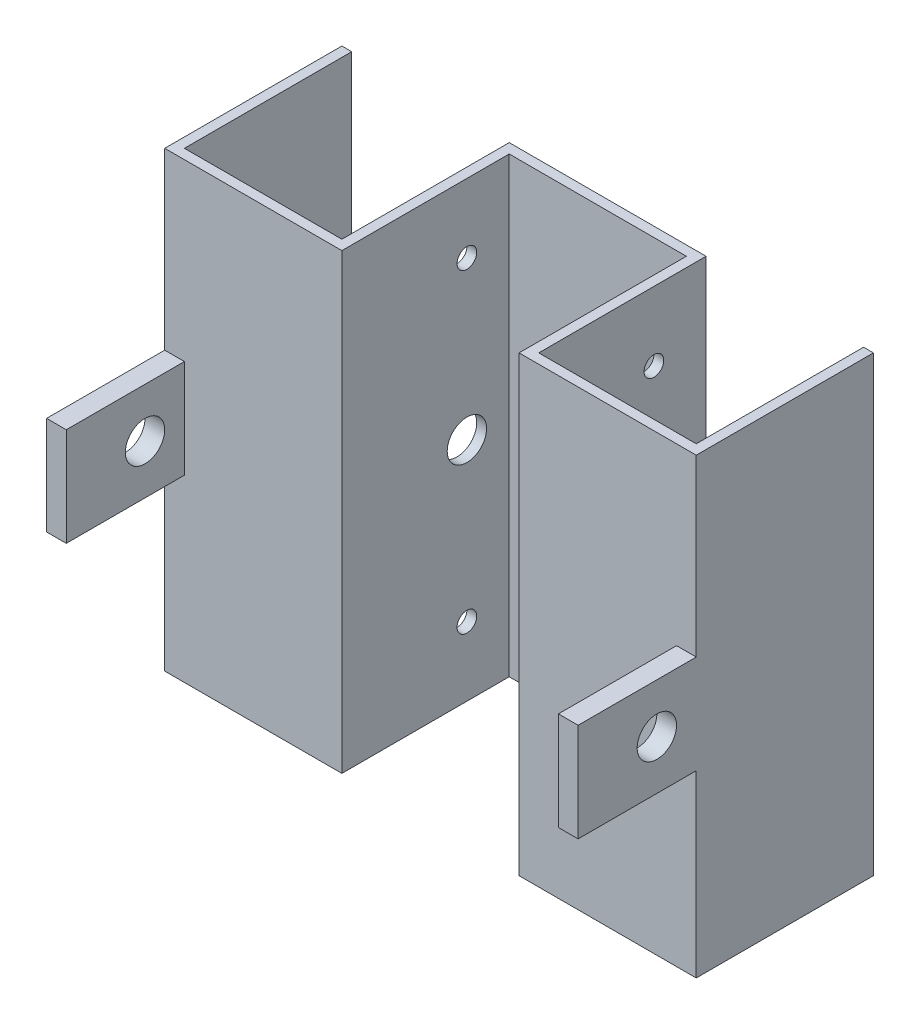
SolidWorks part; units mm, degrees
ref_plane "Plan de face" through (0, 0, 0) normal (0, 0, 1) x (1, 0, 0)
ref_plane "Plan de dessus" through (0, 0, 0) normal (0, 1, 0) x (1, 0, 0)
ref_plane "Plan de droite" through (0, 0, 0) normal (1, 0, 0) x (0, 0, -1)
sketch "Esquisse1" plane through (0, 0, 0) normal (0, 0, 1) x (1, 0, 0)
  line L1 (0, 0) -> (-50, 0)
  line L2 (0, 0) -> (0, 250)
  line L3 (0, 250) -> (-50, 250)
  line L4 (-50, 0) -> (-50, 250)
  dimension "D1" = 250
  dimension "D2" = 50
extrude "Boss.-Extru.1" add sketch "Esquisse1" along normal blind 5
sketch "Esquisse2" plane through (0, 0, 5) normal (0, 0, 1) x (1, 0, 0)
  line L0 (-50, 0) -> (0, 0) construction
  line L1 (-50, 250) -> (-45, 250)
  line L2 (-50, 250) -> (-50, 0)
  line L3 (-50, 0) -> (-45, 0)
  line L4 (-45, 250) -> (-45, 0)
  dimension "D1" = 5
extrude "Boss.-Extru.2" add sketch "Esquisse2" along normal blind 80
sketch "Esquisse3" plane through (0, 0, 85) normal (0, 0, 1) x (1, 0, 0)
  line L1 (-45, 250) -> (-130, 250)
  line L2 (-45, 250) -> (-45, 0)
  line L3 (-45, 0) -> (-130, 0)
  line L4 (-130, 250) -> (-130, 0)
  dimension "D1" = 85
extrude "Boss.-Extru.3" add sketch "Esquisse3" along normal blind 5
sketch "Esquisse4" plane through (-130, 0, 0) normal (-1, 0, 0) x (0, 0, 1)
  line L1 (90, 250) -> (0, 250)
  line L2 (90, 250) -> (90, 0)
  line L3 (90, 0) -> (0, 0)
  line L4 (0, 250) -> (0, 0)
extrude "Boss.-Extru.4" add sketch "Esquisse4" along normal blind 5
sketch "Esquisse5" plane through (-50, 0, 0) normal (-1, 0, 0) x (0, 0, 1)
  line L0 (0, 250) -> (0, 0) construction
  line L1 (0, 0) -> (90, 0) construction
  circle A0 centre (26.5, 125) radius 10
  dimension "D1" = 20
  dimension "D3" = 125
  dimension "D2" = 26.5
extrude "Enlèv. mat.-Extru.1" cut sketch "Esquisse5" against normal blind 5
sketch "Esquisse6" plane through (-50, 0, 0) normal (-1, 0, 0) x (0, 0, 1)
  circle A0 centre (26.5, 125) radius 35
  circle A1 centre (26.5, 205) radius 35
  circle A2 centre (26.5, 45) radius 35
  circle A3 centre (26.5, 205) radius 5
  circle A4 centre (26.5, 45) radius 5
  dimension "D1" = 70
  dimension "D2" = 70
  dimension "D3" = 70
  dimension "D4" = 80
  dimension "D5" = 80
  dimension "D6" = 10
  dimension "D7" = 10
extrude "Enlèv. mat.-Extru.2" cut sketch "Esquisse6" against normal blind 5 contours A3 | A4
mirror "Symétrie2" about plane through (0, 0, 5) normal (-1, 0, 0) of "Enlèv. mat.-Extru.2", "Enlèv. mat.-Extru.1", "Boss.-Extru.4", "Boss.-Extru.3", "Boss.-Extru.2", "Boss.-Extru.1"
sketch "Esquisse7" plane through (-135, 0, 0) normal (-1, 0, 0) x (0, 0, 1)
  line L0 (0, 14.6684) -> (37.1849, 2.7028)
  line L1 (0, 250) -> (0, 0) construction
  line L2 (37.1849, 2.7028) -> (90, 44.1445)
  line L3 (90, 0) -> (90, 250) construction
  line L4 (90, 44.1445) -> (105.1842, 44.1445)
  line L5 (105.1842, 44.1445) -> (105.1842, -34.653)
  line L6 (105.1842, -34.653) -> (101.3902, -34.653)
  line L7 (0, 14.6684) -> (-19.7244, 14.6684)
  line L8 (-19.7244, 14.6684) -> (-19.7244, -34.653)
  line L9 (-19.7244, -34.653) -> (101.3902, -34.653)
sketch "Esquisse8" plane through (135, 0, 0) normal (1, 0, 0) x (0, 0, -1)
  line L4 (-90, 0) -> (-90, 250) construction
  line L5 (-150, 151.192) -> (-90, 101.192) construction
  line L6 (-90, 125) -> (-90, 151.192)
  line L7 (-90, 151.192) -> (-150, 151.192)
  line L8 (-150, 125) -> (-150, 151.192)
  line L9 (-110, 172.4568) -> (-110, 69.7634) construction
  line L11 (-90, 125) -> (-90, 101.192)
  line L12 (-90, 101.192) -> (-150, 101.192)
  line L13 (-150, 125) -> (-150, 101.192)
  circle A0 centre (-110, 126.192) radius 20
  circle A1 centre (-110, 126.192) radius 10
  line M1 (-90, 250) -> (-90, 0)
  dimension "D1" = 60
  dimension "D2" = 50
  dimension "D4" = 40
  dimension "D5" = 20
  dimension "D3" = 20
extrude "Boss.-Extru.5" add sketch "Esquisse8" against normal blind 10 contours L8 L13 L12 L7 A0 M1 | A0 A1
sketch "Esquisse9" plane through (-135, 0, 0) normal (-1, 0, 0) x (0, 0, 1)
  line L1 (90, 151.192) -> (150, 151.192)
  line L2 (90, 151.192) -> (90, 101.192)
  line L3 (90, 101.192) -> (150, 101.192)
  line L4 (150, 151.192) -> (150, 101.192)
  circle A0 centre (110, 126.192) radius 10
extrude "Boss.-Extru.6" add sketch "Esquisse9" against normal blind 10
sketch "Esquisse11" plane through (135, 0, 0) normal (1, 0, 0) x (0, 0, -1)
  line L0 (0, 250) -> (0, 0) construction
  line L1 (-90, 0) -> (0, 0)
  line L2 (-90, 0) -> (-90, 10)
  line L3 (-90, 10) -> (0, 10)
  line L4 (0, 0) -> (0, 10)
  line L6 (-90, 250) -> (0, 250)
  line L7 (-90, 250) -> (-90, 240)
  line L8 (-90, 240) -> (0, 240)
  line L9 (0, 250) -> (0, 240)
  dimension "D1" = 10
  dimension "D2" = 10
extrude "Enlèv. mat.-Extru.6" cut sketch "Esquisse11" against normal through all
